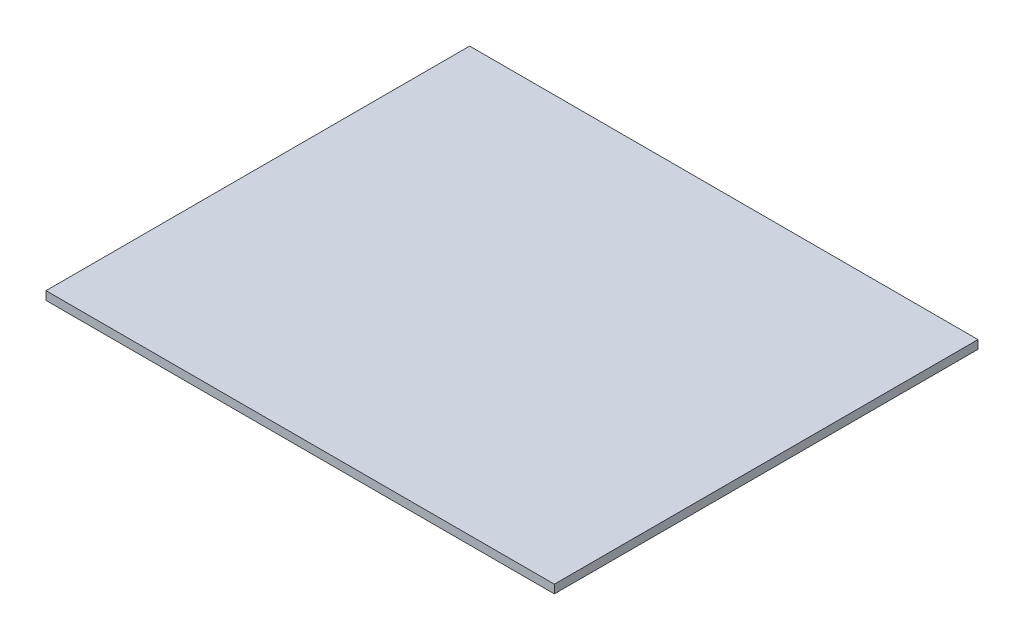
SolidWorks part; units mm, degrees
ref_plane "Front Plane" through (0, 0, 0) normal (0, 0, 1) x (1, 0, 0)
ref_plane "Top Plane" through (0, 0, 0) normal (0, 1, 0) x (1, 0, 0)
ref_plane "Right Plane" through (0, 0, 0) normal (1, 0, 0) x (0, 0, -1)
sketch "Sketch1" plane through (0, 0, 0) normal (0, 1, 0) x (1, 0, 0)
  line L1 (76.2, 63.5) -> (-76.2, 63.5)
  line L2 (76.2, 63.5) -> (76.2, -63.5)
  line L3 (76.2, -63.5) -> (-76.2, -63.5)
  line L4 (-76.2, 63.5) -> (-76.2, -63.5)
  line L5 (76.2, 63.5) -> (-76.2, -63.5) construction
  line L6 (76.2, -63.5) -> (-76.2, 63.5) construction
  point P0 (0, 0)
  dimension "D1" = 152.4
  dimension "D2" = 127
extrude "Boss-Extrude1" add sketch "Sketch1" along normal blind 2.54
